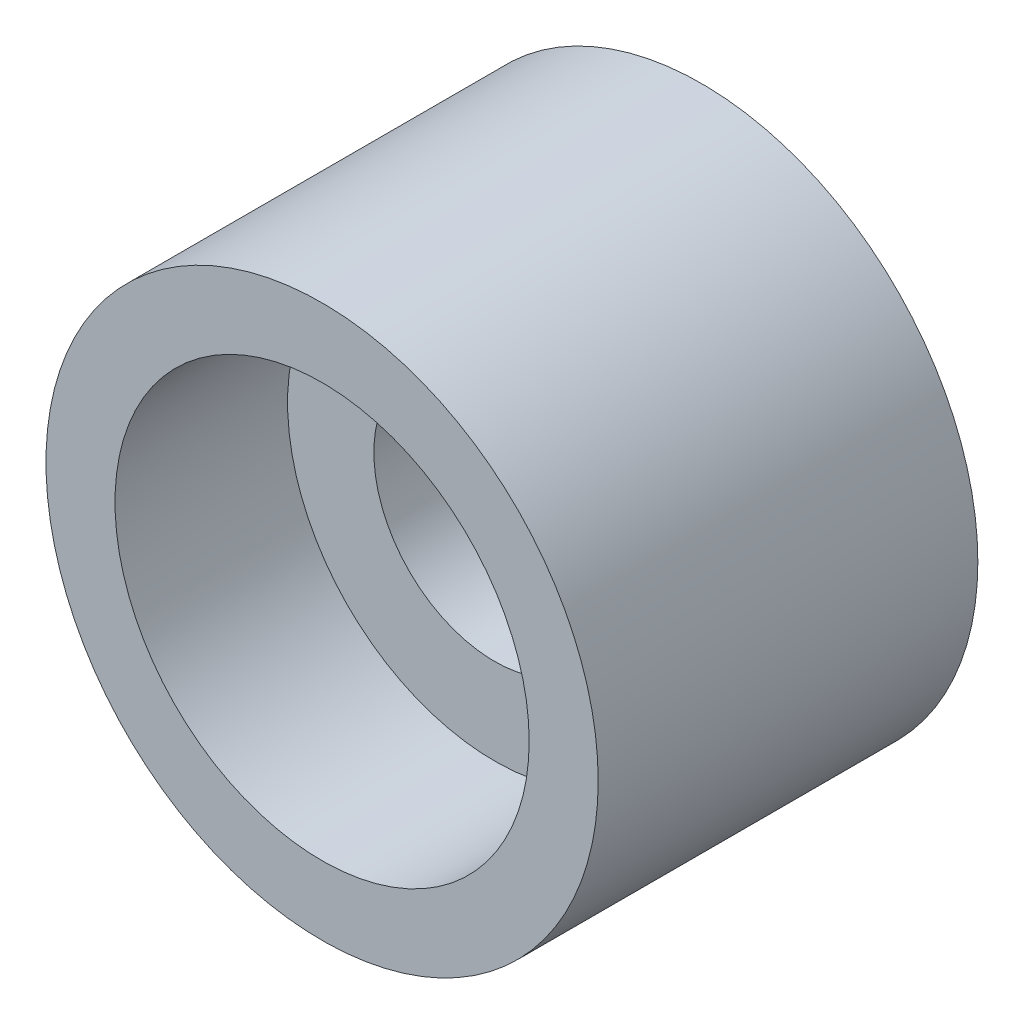
SolidWorks part; units mm, degrees
ref_plane "Front Plane" through (0, 0, 0) normal (0, 0, 1) x (1, 0, 0)
ref_plane "Top Plane" through (0, 0, 0) normal (0, 1, 0) x (1, 0, 0)
ref_plane "Right Plane" through (0, 0, 0) normal (1, 0, 0) x (0, 0, -1)
sketch "Sketch1" plane through (0, 0, 0) normal (0, 0, 1) x (1, 0, 0)
  circle A0 centre (0, 0) radius 1.75
  circle A1 centre (0, 0) radius 4
  dimension "D1" = 3.5
  dimension "D2" = 8
extrude "Boss-Extrude1" add sketch "Sketch1" along normal blind 3
sketch "Sketch2" plane through (0, 0, 3) normal (0, 0, 1) x (1, 0, 0)
  circle A0 centre (0, 0) radius 3
  circle A1 centre (0, 0) radius 4
  dimension "D1" = 1
  dimension "D2" = 6
extrude "Boss-Extrude2" add sketch "Sketch2" along normal blind 2.5
hole_wizard "Tap Drill for M2x0.4 Tap1" positions "3DSketch4" profile "Sketch6" hole size "M2x0.4" standard "ANSI Metric"
sketch3d "3DSketch4"
  point P0 (0.1358, -3.9977, 1.5)
  dimension "D1" = 1.5
sketch "Sketch6" plane through (0.1358, -3.9977, 1.5) normal (0, 0, 1) x (0.9994, 0.034, 0)
  line L0 (0, 0) -> (0, 2.25)
  line L1 (0, 2.25) -> (0.8, 2.25)
  line L2 (0.8, 2.25) -> (0.8, 0)
  line L5 (0.8, 0) -> (0, 0)
  line L11 (0, -6.35) -> (0, 107.95) construction
  dimension "Thru Hole Dia." = 1.6
  dimension "Thru Hole Depth" = 2.25
